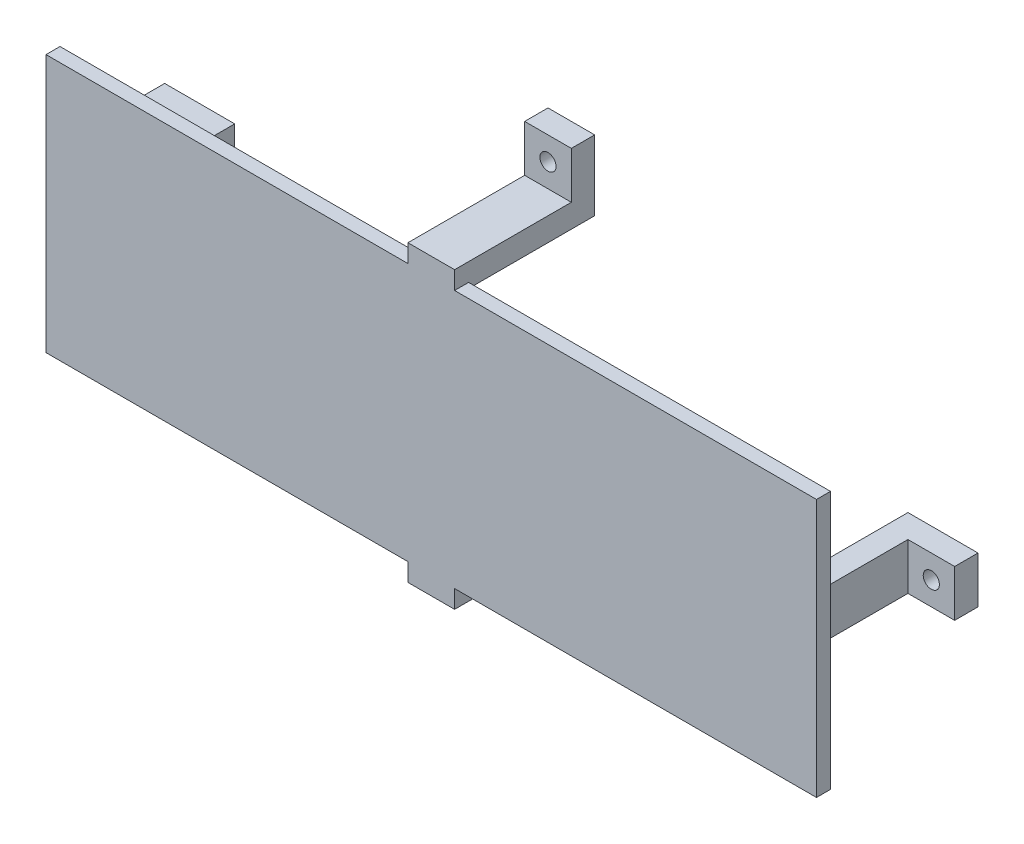
SolidWorks part; units mm, degrees
ref_plane "Front Plane" through (0, 0, 0) normal (0, 0, 1) x (1, 0, 0)
ref_plane "Top Plane" through (0, 0, 0) normal (0, 1, 0) x (1, 0, 0)
ref_plane "Right Plane" through (0, 0, 0) normal (1, 0, 0) x (0, 0, -1)
sketch "Sketch2" plane through (0, 0, 0) normal (0, 0, 1) x (1, 0, 0)
  line L0 (-68.085, -22.5) -> (68.085, 22.5) construction
  line L1 (-68.085, 22.5) -> (68.085, 22.5) construction
  line L2 (-68.085, 22.5) -> (-68.085, -22.5) construction
  line L3 (-68.085, -22.5) -> (68.085, -22.5) construction
  line L4 (68.085, 22.5) -> (68.085, -22.5) construction
  line L5 (-72.085, 26.5) -> (72.085, 26.5) construction
  line L6 (72.085, 26.5) -> (72.085, -26.5) construction
  line L7 (-72.085, -26.5) -> (72.085, -26.5) construction
  line L8 (-72.085, 26.5) -> (-72.085, -26.5) construction
  line L9 (0, 0) -> (-100, 0) construction
  line L10 (-77.085, 5) -> (-72.085, 5)
  line L11 (-77.085, 5) -> (-77.085, -5)
  line L12 (-77.085, -5) -> (-72.085, -5)
  line L13 (-72.085, 5) -> (-72.085, -5)
  line L14 (-5, 31.5) -> (5, 31.5)
  line L15 (-5, 31.5) -> (-5, 26.5)
  line L16 (-5, 26.5) -> (5, 26.5)
  line L17 (5, 31.5) -> (5, 26.5)
  line L18 (0, 0) -> (0, 108.7377) construction
  line L19 (-77.085, 5) -> (-72.085, -5) construction
  line L20 (-5, 26.5) -> (5, 31.5) construction
  line L21 (77.085, -5) -> (72.085, -5)
  line L22 (77.085, 5) -> (77.085, -5)
  line L23 (72.085, 5) -> (72.085, -5)
  line L24 (77.085, 5) -> (72.085, 5)
  line L25 (-5, -26.5) -> (5, -26.5)
  line L26 (-5, -31.5) -> (-5, -26.5)
  line L27 (-5, -31.5) -> (5, -31.5)
  line L28 (5, -31.5) -> (5, -26.5)
  point P4 (0, 0)
  point P23 (-74.585, 0)
  point P25 (0, 29)
  point P34 (0, 108.7377)
  dimension "D1" = 45
  dimension "D2" = 136.17
  dimension "D4" = 5
  dimension "D5" = 10
  dimension "D6" = 5
  dimension "D7" = 10
  dimension "D3" = 4
extrude "Boss-Extrude1" add sketch "Sketch2" along normal blind 27
sketch "Sketch3" plane through (0, 0, 27) normal (0, 0, 1) x (1, 0, 0)
  line L0 (-82.5, 27.64) -> (82.5, -27.64) construction
  line L1 (-82.5, 27.64) -> (82.5, 27.64)
  line L2 (-82.5, 27.64) -> (-82.5, -27.64)
  line L3 (-82.5, -27.64) -> (82.5, -27.64)
  line L4 (82.5, 27.64) -> (82.5, -27.64)
  point P4 (0, 0)
  dimension "D1" = 165
  dimension "D2" = 55.28
extrude "Boss-Extrude2" add sketch "Sketch3" along normal blind 3
sketch "Sketch4" plane through (0, 0, 27) normal (0, 0, 1) x (1, 0, 0)
  line L0 (-5, 27.64) -> (5, 27.64) construction
  line L1 (5, 27.64) -> (5, 31.5) construction
  line L2 (5, 31.5) -> (-5, 31.5) construction
  line L3 (-5, 31.5) -> (-5, 27.64) construction
  line L4 (5, -31.5) -> (5, -27.64) construction
  line L5 (5, -27.64) -> (-5, -27.64) construction
  line L6 (-5, -27.64) -> (-5, -31.5) construction
  line L7 (-5, -31.5) -> (5, -31.5) construction
  line L8 (-5, 27.64) -> (5, 27.64)
  line L9 (5, 27.64) -> (5, 31.5)
  line L10 (5, 31.5) -> (-5, 31.5)
  line L11 (-5, 31.5) -> (-5, 27.64)
  line L12 (5, -31.5) -> (5, -27.64)
  line L13 (5, -27.64) -> (-5, -27.64)
  line L14 (-5, -27.64) -> (-5, -31.5)
  line L15 (-5, -31.5) -> (5, -31.5)
extrude "Boss-Extrude3" add sketch "Sketch4" along normal up to surface (3 mm away) up to face at (0, 0, 30)
sketch "Sketch5" plane through (0, 5, 0) normal (0, 1, 0) x (1, 0, 0)
  line L0 (0, 0) -> (0, -40.7206) construction
  line L1 (-77.085, 0) -> (-87.085, 0)
  line L2 (-77.085, 0) -> (-77.085, -5)
  line L3 (-77.085, -5) -> (-87.085, -5)
  line L4 (-87.085, 0) -> (-87.085, -5)
  line L5 (87.085, 0) -> (87.085, -5)
  line L6 (77.085, 0) -> (87.085, 0)
  line L7 (77.085, 0) -> (77.085, -5)
  line L8 (77.085, -5) -> (87.085, -5)
  dimension "D1" = 5
  dimension "D2" = 10
extrude "Boss-Extrude4" add sketch "Sketch5" against normal up to surface (10 mm away) up to face at (-74.585, -5, 13.5)
sketch "Sketch7" plane through (-5, 0, 0) normal (-1, 0, 0) x (0, 0, 1)
  line L0 (0, 0) -> (45.7182, 0) construction
  line L1 (0, 31.5) -> (5, 31.5)
  line L2 (0, 31.5) -> (0, 41.5)
  line L3 (0, 41.5) -> (5, 41.5)
  line L4 (5, 31.5) -> (5, 41.5)
  line L5 (0, -41.5) -> (5, -41.5)
  line L6 (0, -31.5) -> (0, -41.5)
  line L7 (0, -31.5) -> (5, -31.5)
  line L8 (5, -31.5) -> (5, -41.5)
  dimension "D1" = 5
  dimension "D2" = 10
extrude "Boss-Extrude5" add sketch "Sketch7" against normal up to surface (10 mm away) up to face at (5, -28.5467, 19)
sketch "Sketch8" plane through (0, 0, 5) normal (0, 0, 1) x (1, 0, 0)
  line L0 (-87.085, 5) -> (-77.085, -5) construction
  line L1 (-5, -31.5) -> (5, -41.5) construction
  line L2 (0, 0) -> (0, 49.5906) construction
  line L3 (0, 0) -> (57.6811, 0) construction
  circle A0 centre (-82.085, 0) radius 1.73
  circle A1 centre (0, -36.5) radius 1.73
  circle A2 centre (82.085, 0) radius 1.73
  circle A3 centre (0, 36.5) radius 1.73
  dimension "D1" = 3.46
  dimension "D2" = 3.46
extrude "Cut-Extrude1" cut sketch "Sketch8" against normal through all
